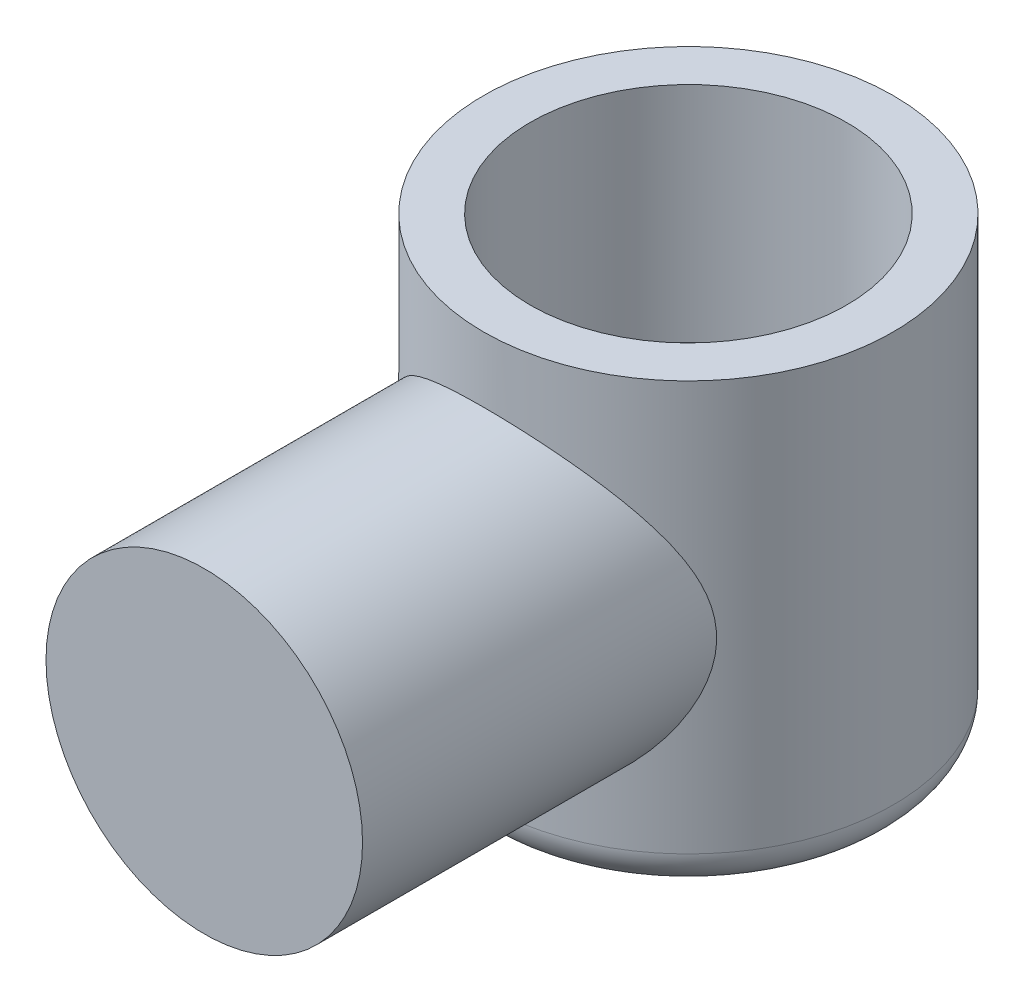
SolidWorks part; units mm, degrees
ref_plane "Front Plane" through (0, 0, 0) normal (0, 0, 1) x (1, 0, 0)
ref_plane "Top Plane" through (0, 0, 0) normal (0, 1, 0) x (1, 0, 0)
ref_plane "Right Plane" through (0, 0, 0) normal (1, 0, 0) x (0, 0, -1)
sketch "Sketch1" plane through (0, 0, 0) normal (0, 1, 0) x (1, 0, 0)
  line L0 (0, -55) -> (0, 55) construction
  line L1 (-55, 0) -> (55, 0) construction
  circle A0 centre (0, 0) radius 55
  dimension "D1" = 110
extrude "Boss-Extrude1" add sketch "Sketch1" along normal mid plane 120
sketch "Sketch2" plane through (0, 0, 0) normal (0, 0, 1) x (1, 0, 0)
  circle A0 centre (0, 0) radius 42.5
  dimension "D1" = 85
extrude "Boss-Extrude2" add sketch "Sketch2" along normal blind 130
fillet "Fillet2" radius 10 1 edges at (0, -60, 55)
sketch "Sketch3" plane through (0, 0, 0) normal (0, 1, 0) x (1, 0, 0)
  circle A0 centre (0, 0) radius 42.5
  dimension "D1" = 85
extrude "Cut-Extrude1" cut sketch "Sketch3" along normal blind 110 contours A0
